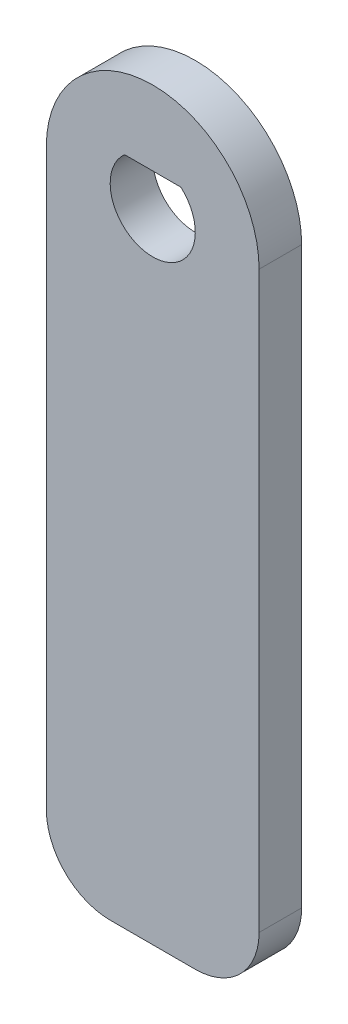
SolidWorks part; units mm, degrees
ref_plane "Front Plane" through (0, 0, 0) normal (0, 0, 1) x (1, 0, 0)
ref_plane "Top Plane" through (0, 0, 0) normal (0, 1, 0) x (1, 0, 0)
ref_plane "Right Plane" through (0, 0, 0) normal (1, 0, 0) x (0, 0, -1)
sketch "Sketch1" plane through (0, 0, 0) normal (0, 0, 1) x (1, 0, 0)
  line L0 (-1.3229, 1.5) -> (1.3229, 1.5)
  line L1 (-5, 0) -> (-5, -27)
  line L2 (-2, -30) -> (2, -30)
  line L3 (5, -27) -> (5, 0)
  arc A0 (-1.3229, 1.5) -> (1.3229, 1.5) centre (0, 0) ccw
  arc A1 (5, 0) -> (-5, 0) centre (0, 0) ccw
  arc A2 (5, -27) -> (2, -30) centre (2, -27) cw
  arc A3 (-2, -30) -> (-5, -27) centre (-2, -27) cw
  point P10 (5, -30)
  dimension "D1" = 4
  dimension "D3" = 10
  dimension "D5" = 3
  dimension "D6" = 3
  dimension "D2" = 1.5
  dimension "D4" = 30
extrude "Boss-Extrude1" add sketch "Sketch1" along normal blind 2
